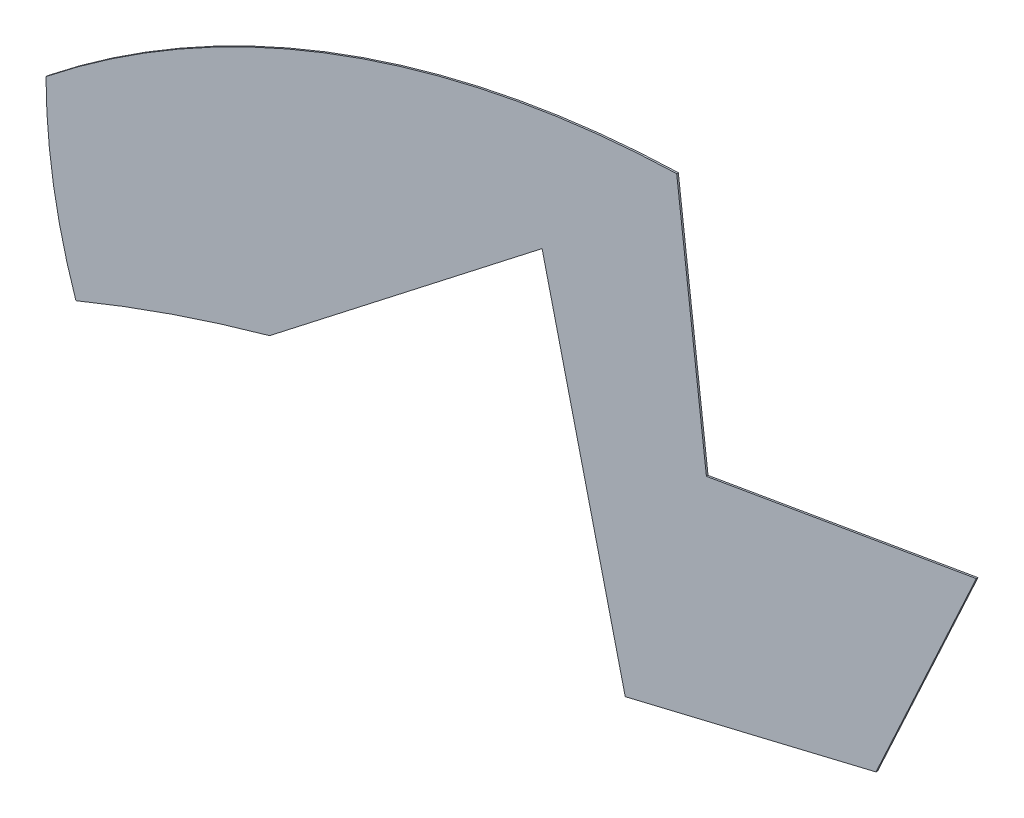
SolidWorks part; units mm, degrees
ref_plane "Alzado" through (0, 0, 0) normal (0, 0, 1) x (1, 0, 0)
ref_plane "Planta" through (0, 0, 0) normal (0, 1, 0) x (1, 0, 0)
ref_plane "Vista lateral" through (0, 0, 0) normal (1, 0, 0) x (0, 0, -1)
sketch "Model" plane through (0, 0, 0) normal (0, 0, 1) x (1, 0, 0)
  line L0 (29.5126, 24.4804) -> (27.7031, 39.5276)
  line L1 (45.9389, 27.3045) -> (29.5126, 24.4804)
  line L2 (39.8319, 14.0606) -> (24.5735, 10.3978)
  line L3 (39.8319, 14.0606) -> (45.9389, 27.3045)
  line L4 (2.9336, 18.6029) -> (19.5126, 31.4804)
  line L5 (19.5126, 31.4804) -> (24.5735, 10.3978)
  arc A0 (27.7031, 39.5276) -> (-10.6739, 25.4538) centre (29.7132, -25.3144) ccw
  arc A1 (2.9336, 18.6029) -> (-8.8542, 14.5525) centre (30.7069, -81.4039) ccw
  arc A2 (-10.6739, 25.4538) -> (-8.8542, 14.5525) centre (23.1618, 25.4994) ccw
extrude "Saliente-Extruir1" add sketch "Model" along normal blind 0.1
